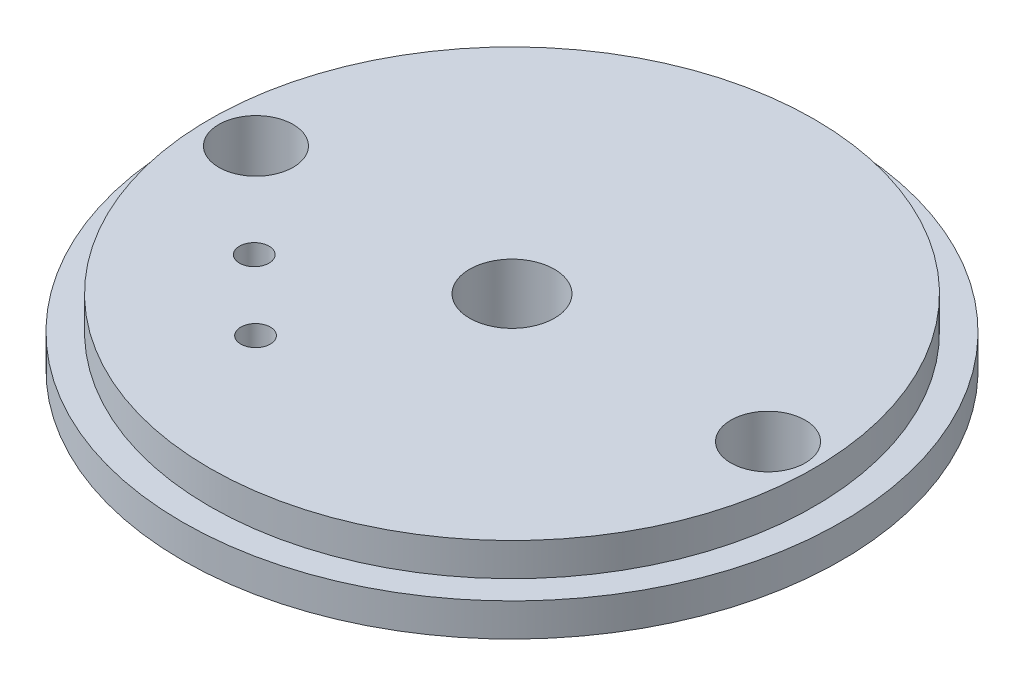
SolidWorks part; units mm, degrees
ref_plane "Front Plane" through (0, 0, 0) normal (0, 0, 1) x (1, 0, 0)
ref_plane "Top Plane" through (0, 0, 0) normal (0, 1, 0) x (1, 0, 0)
ref_plane "Right Plane" through (0, 0, 0) normal (1, 0, 0) x (0, 0, -1)
sketch "Sketch1" plane through (0, 0, 0) normal (0, 1, 0) x (1, 0, 0)
  circle A0 centre (0, 0) radius 25.3365
  dimension "D1" = 50.673
extrude "Boss-Extrude1" add sketch "Sketch1" along normal blind 2.54
sketch "Sketch2" plane through (0, 2.54, 0) normal (0, 1, 0) x (1, 0, 0)
  circle A0 centre (0, 0) radius 23.241
  dimension "D1" = 46.482
extrude "Boss-Extrude2" add sketch "Sketch2" along normal blind 2.54
sketch "Sketch3" plane through (0, 0, 0) normal (0, -1, 0) x (1, 0, 0)
  point P0 (0, 0)
hole_wizard "1/4 Clearance Hole1" positions "Sketch3" profile "Sketch4" hole size "1/4" standard "ANSI Inch" end condition up to next
sketch "Sketch4" plane through (0, 0, 0) normal (1, 0, 0) x (0, 0, -1)
  line L0 (0, 0) -> (0, 5.08)
  line L1 (0, 5.08) -> (3.2639, 5.08)
  line L2 (3.2639, 5.08) -> (3.2639, 0)
  line L5 (3.2639, 0) -> (0, 0)
  line L11 (0, -6.35) -> (0, 107.95) construction
  dimension "Thru Hole Dia." = 6.5278
  dimension "Thru Hole Depth" = 5.08
sketch "Sketch5" plane through (0, 0, 0) normal (0, -1, 0) x (1, 0, 0)
  circle A0 centre (-19.685, 0) radius 2.8575
  circle A1 centre (19.685, 0) radius 2.8575
  point P4 (0, 0)
  point P5 (18.0291, 0)
  point P6 (21.4449, 0)
  point P7 (-19.685, 0)
  point P8 (0, 0)
  point P11 (19.685, 0)
  dimension "D1" = 5.715
extrude "Cut-Extrude1" cut sketch "Sketch5" against normal up to next
sketch "Sketch6" plane through (0, 0, 0) normal (0, -1, 0) x (1, 0, 0)
  arc A0 (-6.1971, 11.9159) -> (-6.2739, 11.8327) centre (-7.0699, 12.6437) ccw construction
  circle A1 centre (-12.5085, 7.3065) radius 1.1364 construction
  circle A2 centre (-7.0699, 12.6437) radius 1.1364
  circle A3 centre (-12.5085, 7.3065) radius 1.1364
extrude "Cut-Extrude2" cut sketch "Sketch6" against normal up to next
